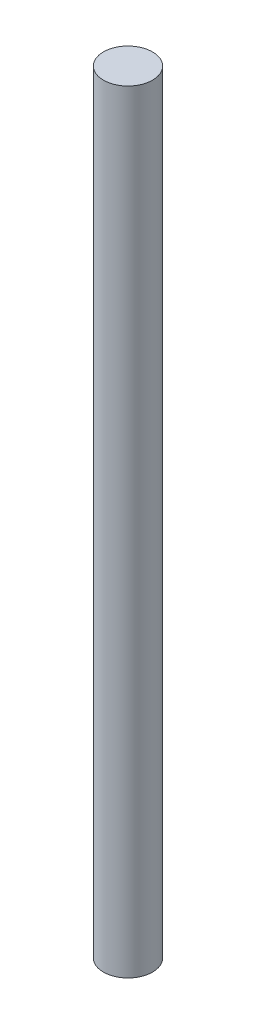
SolidWorks part; units mm, degrees
material "AISI 1010 Steel, hot rolled bar"
ref_plane "Front" through (0, 0, 0) normal (0, 0, 1) x (1, 0, 0)
ref_plane "Top" through (0, 0, 0) normal (0, 1, 0) x (1, 0, 0)
ref_plane "Right" through (0, 0, 0) normal (1, 0, 0) x (0, 0, -1)
sketch "Sketch1" plane through (0, 0, 0) normal (0, 1, 0) x (1, 0, 0)
  circle A0 centre (0, 0) radius 3.175
extrude "Boss-Extrude1" add sketch "Sketch1" along normal blind 100
